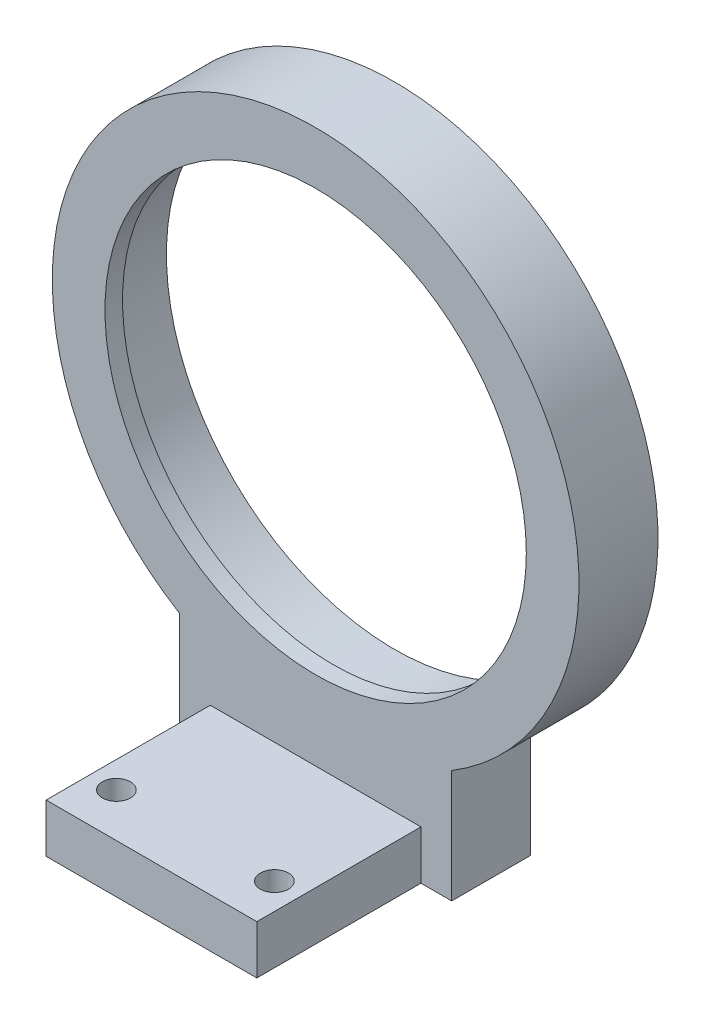
SolidWorks part; units mm, degrees
ref_plane "前视基准面" through (0, 0, 0) normal (0, 0, 1) x (1, 0, 0)
ref_plane "上视基准面" through (0, 0, 0) normal (0, 1, 0) x (1, 0, 0)
ref_plane "右视基准面" through (0, 0, 0) normal (1, 0, 0) x (0, 0, -1)
sketch "草图1" plane through (0, 0, 0) normal (0, 0, 1) x (1, 0, 0)
  line L1 (-15.5, -38) -> (15.5, -38)
  line L2 (-15.5, -38) -> (-15.5, -25.6856)
  line L4 (15.5, -38) -> (15.5, -25.6856)
  line L5 (0, -26) -> (0, -38) construction
  line L6 (-15.5, -31.8428) -> (15.5, -31.8428) construction
  circle A0 centre (0, 0) radius 26
  arc A1 (15.5, -25.6856) -> (-15.5, -25.6856) centre (0, 0) ccw
  point P4 (0, -31.8428)
  dimension "D1" = 52
  dimension "D2" = 60
  dimension "D3" = 31
  dimension "D4" = 38
extrude "凸台-拉伸1" add sketch "草图1" along normal blind 7
sketch "草图4" plane through (0, 0, 7) normal (0, 0, 1) x (1, 0, 0)
  circle A0 centre (0, 0) radius 30
  circle A1 centre (0, 0) radius 24
  dimension "D1" = 60
  dimension "D2" = 48
extrude "凸台-拉伸4" add sketch "草图4" along normal blind 2
sketch "草图5" plane through (0, 0, 7) normal (0, 0, 1) x (1, 0, 0)
  line L12 (0, 0) -> (0, -44.0886) construction
  line L13 (-15.5, -38) -> (15.5, -38) construction
  line L14 (-12, -33) -> (12, -33)
  line L15 (-12, -33) -> (-12, -38)
  line L16 (-12, -38) -> (12, -38)
  line L17 (12, -33) -> (12, -38)
  dimension "D1" = 24
  dimension "D2" = 5
extrude "凸台-拉伸5" add sketch "草图5" along normal blind 20.7
sketch "草图6" plane through (0, 0, 7) normal (0, 0, 1) x (1, 0, 0)
  line L1 (15.5, -38) -> (15.5, -25.6856) construction
  line L2 (-15.5, -25.6856) -> (-15.5, -38) construction
  line L4 (15.5, -38) -> (15.5, -25.6856)
  line L5 (-15.5, -25.6856) -> (-15.5, -38)
  line L6 (12, -38) -> (15.5, -38) construction
  line L7 (12, -38) -> (12, -33) construction
  line L8 (12, -33) -> (-12, -33) construction
  line L9 (-12, -33) -> (-12, -38) construction
  line L10 (-15.5, -38) -> (-12, -38) construction
  line L11 (12, -38) -> (15.5, -38)
  line L12 (12, -38) -> (12, -33)
  line L13 (12, -33) -> (-12, -33)
  line L14 (-12, -33) -> (-12, -38)
  line L15 (-15.5, -38) -> (-12, -38)
  circle A0 centre (0, 0) radius 30 construction
  arc A1 (-15.5, -25.6856) -> (15.5, -25.6856) centre (0, 0) ccw
extrude "凸台-拉伸8" add sketch "草图6" along normal up to surface (2 mm away) up to face at (30, 0, 9)
sketch "草图9" plane through (0, -33, 0) normal (0, 1, 0) x (1, 0, 0)
  line L0 (0, 0) -> (0, -35.5963) construction
  line L2 (12, -27.7) -> (-12, -27.7) construction
  circle A0 centre (-9, -22.7) radius 1.6
  circle A1 centre (9, -22.7) radius 1.6
  dimension "D1" = 18
  dimension "D2" = 5
  dimension "D3" = 3.2
extrude "切除-拉伸1" cut sketch "草图9" against normal through all
sketch "草图10" plane through (0, -38, 0) normal (0, -1, 0) x (1, 0, 0)
  line L8 (15.5, 0) -> (15.5, 9)
  line L9 (15.5, 9) -> (12, 9)
  line L10 (12, 9) -> (12, 27.7)
  line L11 (12, 27.7) -> (-12, 27.7)
  line L12 (-12, 27.7) -> (-12, 9)
  line L13 (-12, 9) -> (-15.5, 9)
  line L14 (-15.5, 9) -> (-15.5, 0)
  line L15 (-15.5, 0) -> (15.5, 0)
  line L16 (15.5, 0) -> (15.5, 9)
  line L17 (15.5, 9) -> (12, 9)
  line L18 (12, 9) -> (12, 27.7)
  line L19 (12, 27.7) -> (-12, 27.7)
  line L20 (-12, 27.7) -> (-12, 9)
  line L21 (-12, 9) -> (-15.5, 9)
  line L22 (-15.5, 9) -> (-15.5, 0)
  line L23 (-15.5, 0) -> (15.5, 0)
  dimension "D1" = 0
extrude "凸台-拉伸9" add sketch "草图10" along normal blind 0.56
sketch "草图11" plane through (0, -33, 0) normal (0, 1, 0) x (1, 0, 0)
  circle A0 centre (9, -22.7) radius 1.6 construction
  circle A1 centre (-9, -22.7) radius 1.6 construction
  circle A2 centre (9, -22.7) radius 1.6
  circle A3 centre (-9, -22.7) radius 1.6
extrude "切除-拉伸2" cut sketch "草图11" against normal blind 25
